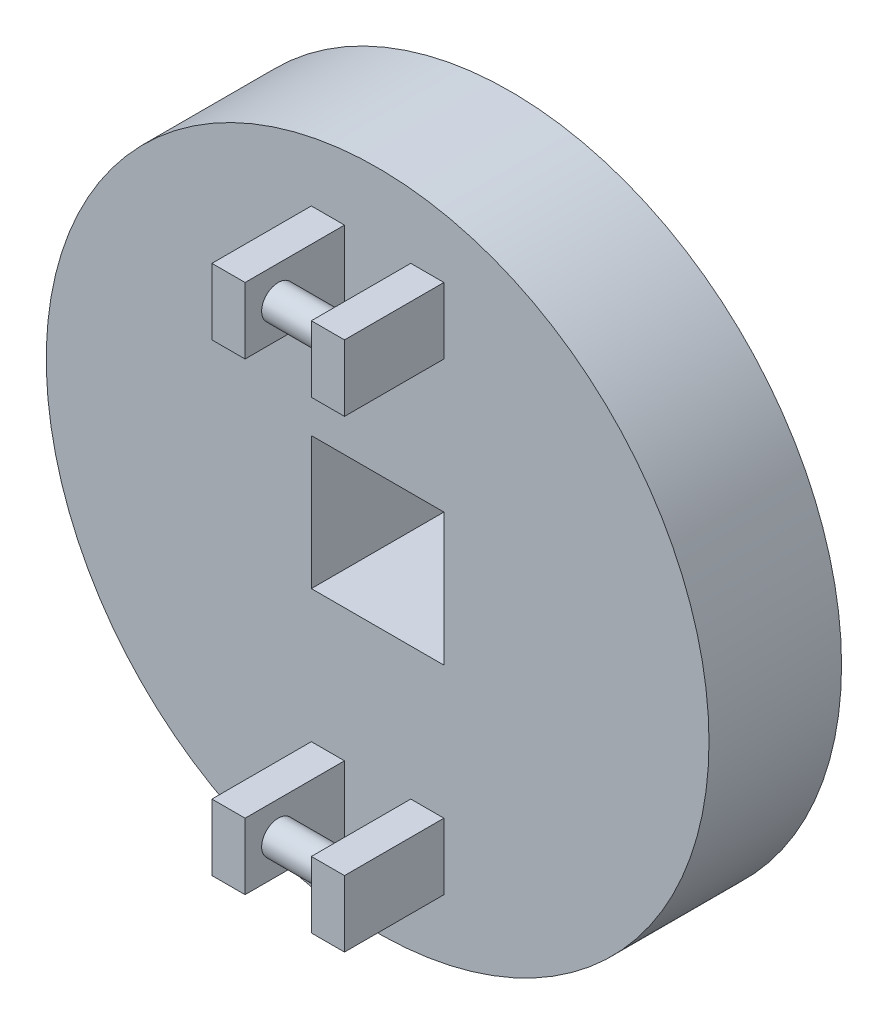
SolidWorks part; units mm, degrees
ref_plane "Front Plane" through (0, 0, 0) normal (0, 0, 1) x (1, 0, 0)
ref_plane "Top Plane" through (0, 0, 0) normal (0, 1, 0) x (1, 0, 0)
ref_plane "Right Plane" through (0, 0, 0) normal (1, 0, 0) x (0, 0, -1)
sketch "Sketch1" plane through (0, 0, 0) normal (0, 0, 1) x (1, 0, 0)
  circle A0 centre (0, 0) radius 63.5
  dimension "D1" = 127
extrude "Boss-Extrude1" add sketch "Sketch1" along normal mid plane 25.4
sketch "Sketch3" plane through (0, 0, 12.7) normal (0, 0, 1) x (1, 0, 0)
  line L0 (-6.35, 50.8) -> (-6.35, 38.1)
  line L1 (-12.7, 38.1) -> (12.7, 38.1)
  line L2 (-12.7, 38.1) -> (-12.7, 50.8)
  line L3 (-12.7, 50.8) -> (12.7, 50.8)
  line L4 (12.7, 38.1) -> (12.7, 50.8)
  line L5 (6.35, 50.8) -> (6.35, 38.1)
  point P4 (0, 38.1)
  point P7 (0, 50.8)
  dimension "D1" = 25.4
  dimension "D2" = 12.7
  dimension "D3" = 38.1
  dimension "D4" = 6.35
  dimension "D5" = 6.35
extrude "Boss-Extrude2" add sketch "Sketch3" along normal blind 19.05 contours L3 L2 L1 L0 | L3 L5 L1 L4
sketch "Sketch4" plane through (-6.35, 0, 0) normal (1, 0, 0) x (0, 0, -1)
  line L0 (-31.75, 50.8) -> (-12.7, 50.8) construction
  line L1 (-31.75, 38.1) -> (-31.75, 50.8) construction
  circle A0 centre (-25.4, 44.45) radius 3.175
  dimension "D1" = 6.35
  dimension "D2" = 6.35
  dimension "D3" = 6.35
extrude "Boss-Extrude3" add sketch "Sketch4" along normal up to next (12.7 mm away)
mirror "Mirror1" about plane through (0, 0, 0) normal (0, 1, 0) of "Boss-Extrude3", "Boss-Extrude2"
sketch "Sketch5" plane through (0, 0, 12.7) normal (0, 0, 1) x (1, 0, 0)
  line L1 (-12.7, -12.7) -> (12.7, -12.7)
  line L2 (-12.7, -12.7) -> (-12.7, 12.7)
  line L3 (-12.7, 12.7) -> (12.7, 12.7)
  line L4 (12.7, -12.7) -> (12.7, 12.7)
  point P4 (12.7, 0)
  point P6 (0, 12.7)
  dimension "D1" = 25.4
  dimension "D2" = 25.4
extrude "Cut-Extrude1" cut sketch "Sketch5" against normal through all
